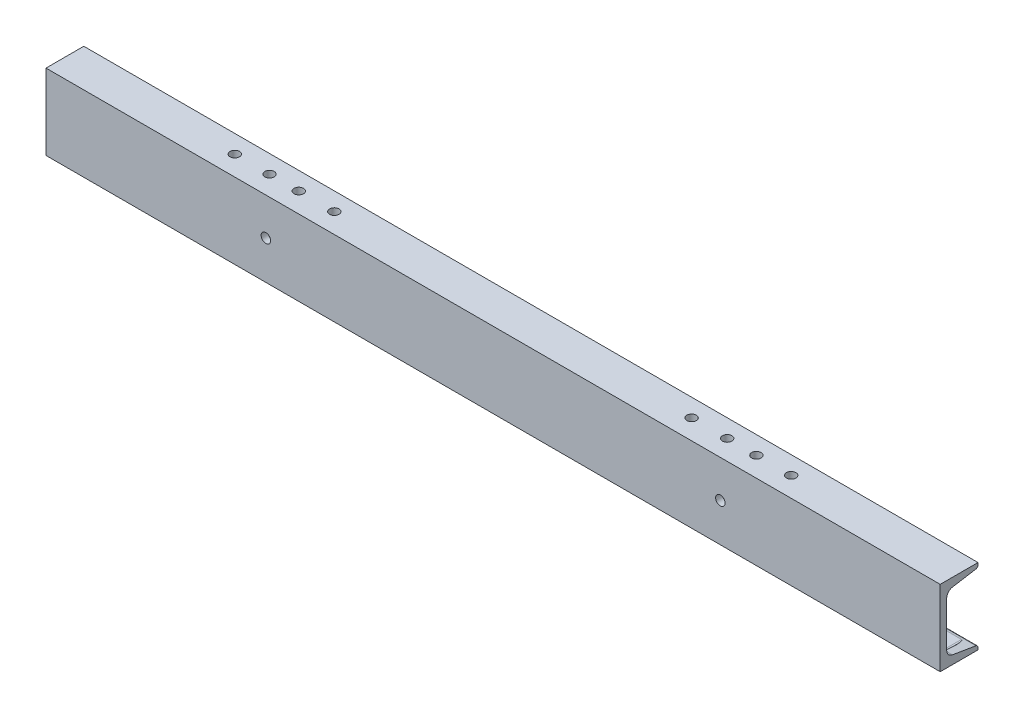
SolidWorks part; units mm, degrees
material "Plain Carbon Steel"
ref_plane "Front Plane" through (0, 0, 0) normal (0, 0, 1) x (1, 0, 0)
ref_plane "Top Plane" through (0, 0, 0) normal (0, 1, 0) x (1, 0, 0)
ref_plane "Right Plane" through (0, 0, 0) normal (1, 0, 0) x (0, 0, -1)
sketch "Sketch1" plane through (0, 0, 0) normal (0, 1, 0) x (1, 0, 0)
  line L0 (-450, 0) -> (450, 0)
  dimension "D1" = 900
other "Structural Member1"
ref_plane "Plane1" through (-450, 0, 0) normal (1, 0, 0) x (0, 0, -1)
sketch "Sketch11" plane through (-450, 0, 0) normal (1, 0, 0) x (0, 0, -1)
  line L0 (0, -38.1) -> (0, 38.1)
  line L1 (0, 38.1) -> (38.0492, 38.1)
  line L2 (0, -38.1) -> (38.0492, -38.1)
  line L5 (31.75, -31.1658) -> (6.35, -31.1658) construction
  line L6 (0, 0) -> (6.5532, 0) construction
  line L12 (6.5532, 22.7314) -> (6.5532, -22.7314)
  line L15 (38.0492, 38.1) -> (38.0492, 35.9423)
  line L16 (38.0492, -38.1) -> (38.0492, -35.9423)
  line L17 (12.2837, 29.4961) -> (35.9268, 33.4369)
  line L18 (12.2837, -29.4961) -> (35.9268, -33.4369)
  arc A9 (6.5532, -22.7314) -> (12.2837, -29.4961) centre (13.4112, -22.7314) ccw
  arc A10 (6.5532, 22.7314) -> (12.2837, 29.4961) centre (13.4112, 22.7314) cw
  arc A11 (38.0492, 35.9423) -> (35.9268, 33.4369) centre (35.5092, 35.9423) cw
  arc A12 (38.0492, -35.9423) -> (35.9268, -33.4369) centre (35.5092, -35.9423) ccw
  point P4 (38.0492, 33.7907)
  point P5 (38.0492, -33.7907)
  point P6 (3.2766, 0)
  point P7 (19.0246, 38.1)
  point P12 (19.0246, -38.1)
  point P13 (0, 0)
  dimension "RI" = 6.858
  dimension "D2" = 9.463
  dimension "RA" = 2.54
  dimension "Depth" = 76.2
  dimension "BF" = 38.0492
  dimension "TW" = 6.5532
  dimension "flange" = 2.1577
  dimension "TF" = 6.9342
sketch "Sketch12" plane through (0, 0, 0) normal (0, 1, 0) x (1, 0, 0)
  line L0 (-412.5239, 20) -> (413.742, 20) construction
  line L1 (-450, 0) -> (450, 0) construction
  line L2 (0, 0) -> (0, 45.9021) construction
  line L3 (-450, 38.0492) -> (-450, 0) construction
  circle A0 centre (-425, 20) radius 4.7625
  circle A1 centre (425, 20) radius 4.7625
  dimension "D2" = 9.525
  dimension "D1" = 20
  dimension "D3" = 25
extrude "Cut-Extrude1" cut sketch "Sketch12" against normal through all
sketch "Sketch15" plane through (0, 0, -6.5532) normal (0, 0, -1) x (-1, 0, 0)
  line L0 (-425, -21.1359) -> (-425, -40.4286) construction
  line L1 (-375.1366, -28.1) -> (-474.8634, -28.1) construction
  line L2 (-450, -38.1) -> (450, -38.1) construction
  line L3 (-412.5, -28.1) -> (-437.5, -28.1) construction
  line L4 (-412.5, -33.1) -> (-437.5, -33.1)
  line L5 (-412.5, -23.1) -> (-437.5, -23.1)
  line L6 (0, 0) -> (0, -58.1771) construction
  line L7 (412.5, -28.1) -> (437.5, -28.1) construction
  line L8 (412.5, -33.1) -> (437.5, -33.1)
  line L9 (412.5, -23.1) -> (437.5, -23.1)
  arc A0 (-412.5, -33.1) -> (-412.5, -23.1) centre (-412.5, -28.1) ccw
  arc A1 (-437.5, -23.1) -> (-437.5, -33.1) centre (-437.5, -28.1) ccw
  arc A2 (412.5, -33.1) -> (412.5, -23.1) centre (412.5, -28.1) cw
  arc A3 (437.5, -23.1) -> (437.5, -33.1) centre (437.5, -28.1) cw
  ellipse E0 centre (-425, -30.7822) end of major axis (-429.7625, -30.7822) minor radius 0.7938 construction
  point P0 (-425, -30.7822)
  point P11 (-425, -28.1)
  point P16 (-425, -28.1)
  point P26 (425, -28.1)
  dimension "D2" = 5
  dimension "D1" = 10
  dimension "D3" = 25
extrude "Cut-Extrude2" cut sketch "Sketch15" along normal blind 40
sketch "Sketch16" plane through (0, 0, 0) normal (0, 1, 0) x (1, 0, 0)
  line L0 (0, -46.4014) -> (0, 86.4014) construction
  line L1 (-394.0256, 20) -> (394.0256, 20) construction
  line L2 (450, 0) -> (-450, 0) construction
  circle A0 centre (-215.6, 20) radius 4.7625
  circle A1 centre (-179.8, 20) radius 4.7625
  circle A2 centre (179.8, 20) radius 4.7625
  circle A3 centre (215.6, 20) radius 4.7625
  circle A4 centre (-245, 20) radius 4.7625
  circle A5 centre (-280, 20) radius 4.7625
  circle A6 centre (245, 20) radius 4.7625
  circle A7 centre (280, 20) radius 4.7625
  point P5 (0, 20)
  point P6 (0, 20)
  dimension "D2" = 9.525
  dimension "D1" = 20
  dimension "D3" = 215.6
  dimension "D4" = 35.8
  dimension "D5" = 35
  dimension "D6" = 280
extrude "Cut-Extrude3" cut sketch "Sketch16" along normal through all
sketch "Sketch17" plane through (0, 0, 0) normal (0, 0, 1) x (1, 0, 0)
  circle A0 centre (228.7, 0.6) radius 4.7625 construction
  circle A1 centre (228.7, 0.6) radius 4.7625
  circle A2 centre (-228.7, 0.6) radius 4.7625 construction
  circle A3 centre (-228.7, 0.6) radius 4.7625
extrude "Cut-Extrude4" cut sketch "Sketch17" against normal through all
